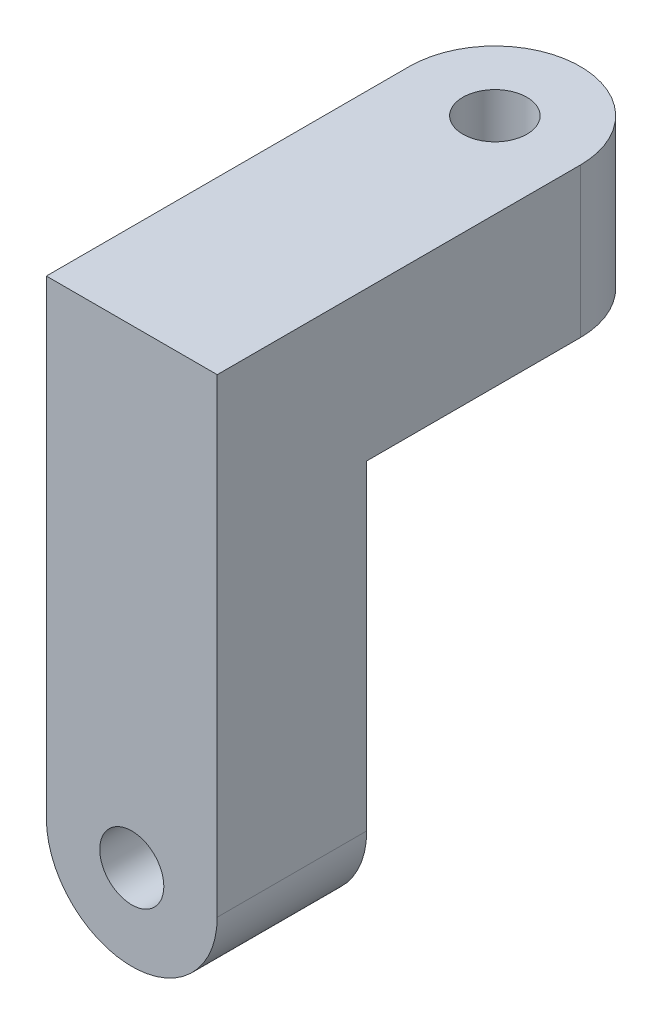
SolidWorks part; units mm, degrees
ref_plane "Front Plane" through (0, 0, 0) normal (0, 0, 1) x (1, 0, 0)
ref_plane "Top Plane" through (0, 0, 0) normal (0, 1, 0) x (1, 0, 0)
ref_plane "Right Plane" through (0, 0, 0) normal (1, 0, 0) x (0, 0, -1)
sketch "Sketch2" plane through (0, 0, 0) normal (0, 0, 1) x (1, 0, 0)
  line L1 (-4, -15) -> (-4, 0)
  line L2 (-4, 0) -> (4, 0)
  line L3 (4, 0) -> (4, -15)
  circle A0 centre (0, -15) radius 1.5
  arc A1 (-4, -15) -> (4, -15) centre (0, -15) ccw
extrude "Boss-Extrude1" add sketch "Sketch2" along normal blind 7
sketch "Sketch3" plane through (0, 0, 0) normal (0, 1, 0) x (1, 0, 0)
  line L0 (0, 0) -> (0, 10)
  line L1 (-4, 10) -> (-4, -7)
  line L2 (-4, -7) -> (4, -7)
  line L3 (4, -7) -> (4, 10)
  circle A0 centre (0, 10) radius 1.5
  arc A1 (4, 10) -> (-4, 10) centre (0, 10) ccw
extrude "Boss-Extrude2" add sketch "Sketch3" along normal blind 7
sketch "Sketch4" plane through (0, 7, 0) normal (0, 1, 0) x (1, 0, 0)
  circle A0 centre (0, 10) radius 2
